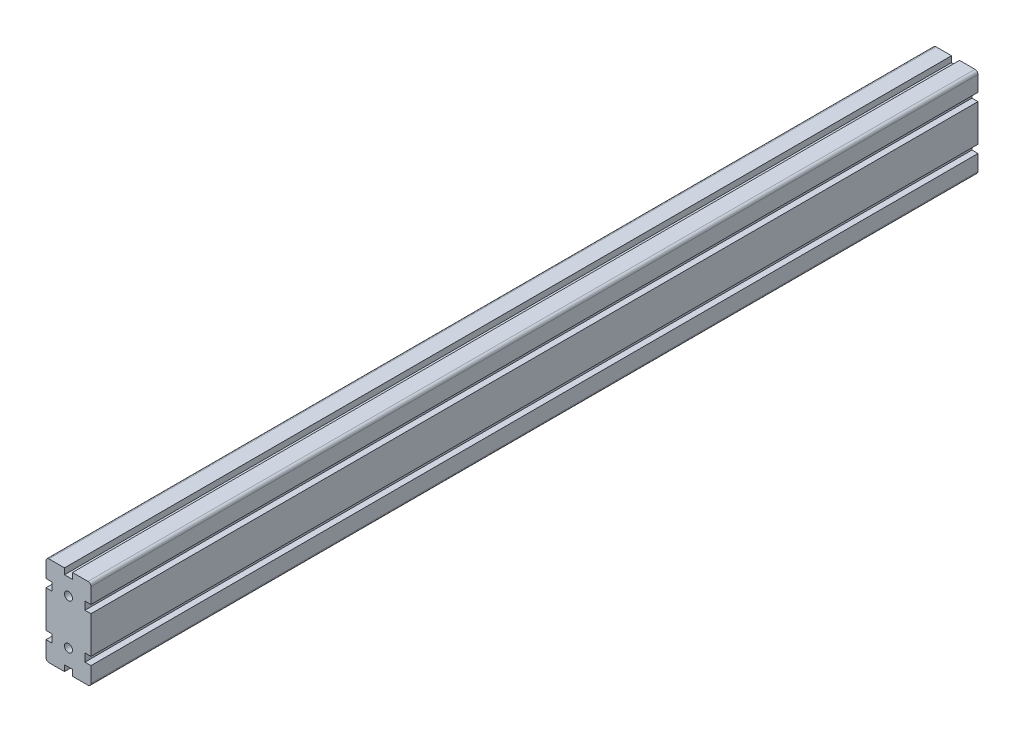
SolidWorks part; units mm, degrees
ref_plane "Plan de face" through (0, 0, 0) normal (0, 0, 1) x (1, 0, 0)
ref_plane "Plan de dessus" through (0, 0, 0) normal (0, 1, 0) x (1, 0, 0)
ref_plane "Plan de droite" through (0, 0, 0) normal (1, 0, 0) x (0, 0, -1)
ref_plane "Plan1" through (0, 0, -1000) normal (0, 0, -1) x (-1, 0, 0)
sketch "Esquisse1" plane through (0, 0, -1000) normal (0, 0, -1) x (-1, 0, 0)
  line L0 (16.5, 26.5) -> (22.5, 26.5)
  line L1 (22.5, 26.5) -> (22.5, 42)
  line L2 (19.5, 45) -> (4, 45)
  line L3 (4, 45) -> (4, 39)
  line L4 (0, 22.5) -> (0, -22.5) construction
  line L5 (0, 22.5) -> (12.9679, 22.5) construction
  line L6 (0, -22.5) -> (12.9679, -22.5) construction
  line L7 (-4, 39) -> (-4, 45)
  line L8 (-4, 45) -> (-19.5, 45)
  line L9 (-22.5, 42) -> (-22.5, 26.5)
  line L10 (-22.5, 26.5) -> (-16.5, 26.5)
  line L11 (-16.5, 18.5) -> (-22.5, 18.5)
  line L12 (-22.5, 18.5) -> (-22.5, -18.5)
  line L13 (-4, -39) -> (4, -39)
  line L14 (16.5, -18.5) -> (16.5, -26.5)
  line L15 (-16.5, -18.5) -> (-16.5, -26.5)
  line L16 (16.5, 26.5) -> (16.5, 18.5)
  line L17 (-22.5, -18.5) -> (-16.5, -18.5)
  line L18 (-16.5, -26.5) -> (-22.5, -26.5)
  line L19 (-22.5, -26.5) -> (-22.5, -42)
  line L20 (-19.5, -45) -> (-4, -45)
  line L21 (-4, -45) -> (-4, -39)
  line L22 (4, -39) -> (4, -45)
  line L23 (4, -45) -> (19.5, -45)
  line L24 (22.5, -42) -> (22.5, -26.5)
  line L25 (22.5, -26.5) -> (16.5, -26.5)
  line L26 (16.5, -18.5) -> (22.5, -18.5)
  line L27 (-16.5, 26.5) -> (-16.5, 18.5)
  line L28 (-4, 39) -> (4, 39)
  line L29 (22.5, -18.5) -> (22.5, 18.5)
  line L30 (22.5, 18.5) -> (16.5, 18.5)
  arc A0 (22.5, 42) -> (19.5, 45) centre (19.5, 42) ccw
  arc A1 (-19.5, 45) -> (-22.5, 42) centre (-19.5, 42) ccw
  arc A2 (-22.5, -42) -> (-19.5, -45) centre (-19.5, -42) ccw
  arc A3 (19.5, -45) -> (22.5, -42) centre (19.5, -42) ccw
  circle A4 centre (0, 22.5) radius 4
  circle A5 centre (0, -22.5) radius 4
  dimension "D3" = 8
  dimension "D4" = 8
  dimension "D1" = 4
  dimension "D2" = 4
extrude "Boss.-Extru.1" add sketch "Esquisse1" against normal blind 888
